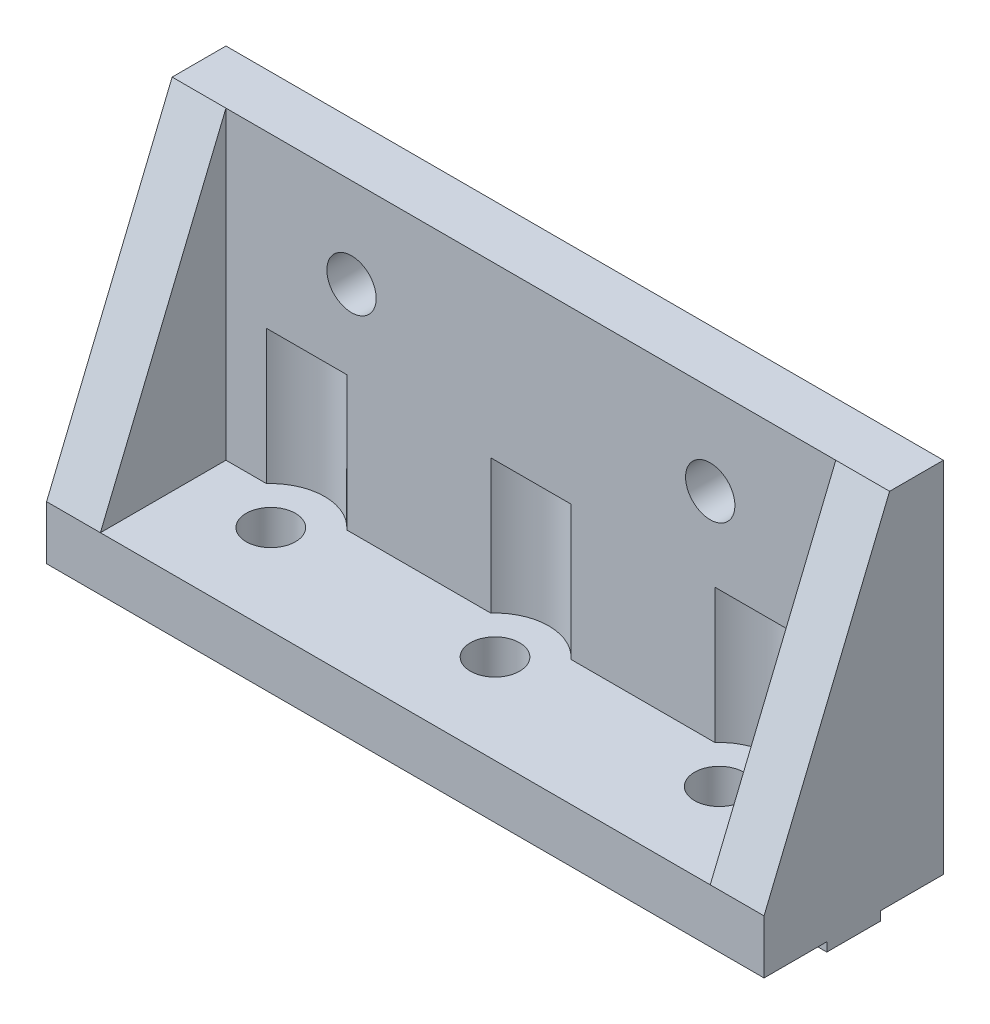
SolidWorks part; units mm, degrees
ref_plane "Alzado" through (0, 0, 0) normal (0, 0, 1) x (1, 0, 0)
ref_plane "Planta" through (0, 0, 0) normal (0, 1, 0) x (1, 0, 0)
ref_plane "Vista lateral" through (0, 0, 0) normal (1, 0, 0) x (0, 0, -1)
sketch "Croquis1" plane through (0, 0, 0) normal (0, 0, 1) x (1, 0, 0)
  line L1 (0, 0) -> (80, 0)
  line L2 (0, 0) -> (0, -40)
  line L3 (0, -40) -> (80, -40)
  line L4 (80, 0) -> (80, -40)
  dimension "D1" = 40
  dimension "D2" = 80
extrude "Saliente-Extruir1" add sketch "Croquis1" along normal blind 20
sketch "Croquis2" plane through (0, 0, 0) normal (0, 1, 0) x (1, 0, 0)
  line L0 (80, -20) -> (0, -20) construction
  line L1 (6, -20) -> (74, -20)
  line L2 (6, -20) -> (6, -6)
  line L3 (6, -6) -> (74, -6)
  line L4 (74, -20) -> (74, -6)
  line L5 (0, -20) -> (0, 0) construction
  line L6 (80, -20) -> (80, 0) construction
  line L7 (80, 0) -> (0, 0) construction
  dimension "D1" = 6
  dimension "D2" = 6
  dimension "D3" = 6
extrude "Cortar-Extruir1" cut sketch "Croquis2" against normal blind 34
sketch "Croquis3" plane through (0, 0, 0) normal (-1, 0, 0) x (0, 0, 1)
  line L0 (20, 0) -> (20, -34)
  line L1 (20, 0) -> (20, -40) construction
  line L2 (20, -34) -> (6, 0)
  line L3 (20, 0) -> (0, 0) construction
  line L4 (6, 0) -> (20, 0)
  dimension "D1" = 14
  dimension "D2" = 34
extrude "Cortar-Extruir2" cut sketch "Croquis3" against normal up to surface (80 mm away) up to face at (80, -20, 10)
sketch "Croquis4" plane through (0, 0, 0) normal (0, 0, -1) x (-1, 0, 0)
  line L0 (-80, 0) -> (0, 0) construction
  line L1 (0, 0) -> (0, -40) construction
  circle A0 centre (-60, -10) radius 2.75
  circle A1 centre (-20, -10) radius 2.75
  dimension "D1" = 5.5
  dimension "D2" = 5.5
  dimension "D3" = 10
  dimension "D4" = 10
  dimension "D5" = 20
  dimension "D6" = 60
extrude "Cortar-Extruir3" cut sketch "Croquis4" against normal up to next
sketch "Croquis5" plane through (0, -40, 0) normal (0, -1, 0) x (1, 0, 0)
  line L0 (0, 20) -> (80, 20) construction
  line L1 (80, 20) -> (80, 0) construction
  circle A0 centre (15, 10) radius 2.75
  circle A1 centre (40, 10) radius 2.75
  circle A2 centre (65, 10) radius 2.75
  dimension "D1" = 5.5
  dimension "D2" = 5.5
  dimension "D3" = 5.5
  dimension "D4" = 10
  dimension "D5" = 10
  dimension "D6" = 10
  dimension "D7" = 40
  dimension "D8" = 25
  dimension "D9" = 25
sketch "Croquis8" plane through (0, -40, 0) normal (0, -1, 0) x (1, 0, 0)
  line L0 (0, 20) -> (0, 0) construction
  line L1 (0, 13) -> (80, 13)
  line L2 (0, 13) -> (0, 7)
  line L3 (0, 7) -> (80, 7)
  line L4 (80, 13) -> (80, 7)
  line L5 (80, 20) -> (80, 0) construction
  line L6 (0, 20) -> (80, 20) construction
  point P8 (0, 10)
  dimension "D1" = 6
  dimension "D2" = 10
extrude "Saliente-Extruir2" add sketch "Croquis8" along normal blind 1
extrude "Cortar-Extruir6" cut sketch "Croquis5" against normal through all both and the other way through all
sketch "Croquis9" plane through (0, -34, 0) normal (0, 1, 0) x (1, 0, 0)
  circle A0 centre (15, -10) radius 6
  circle A1 centre (40, -10) radius 6
  circle A2 centre (65, -10) radius 6
  dimension "D1" = 12
  dimension "D2" = 12
  dimension "D3" = 12
extrude "Cortar-Extruir8" cut sketch "Croquis9" along normal blind 15
